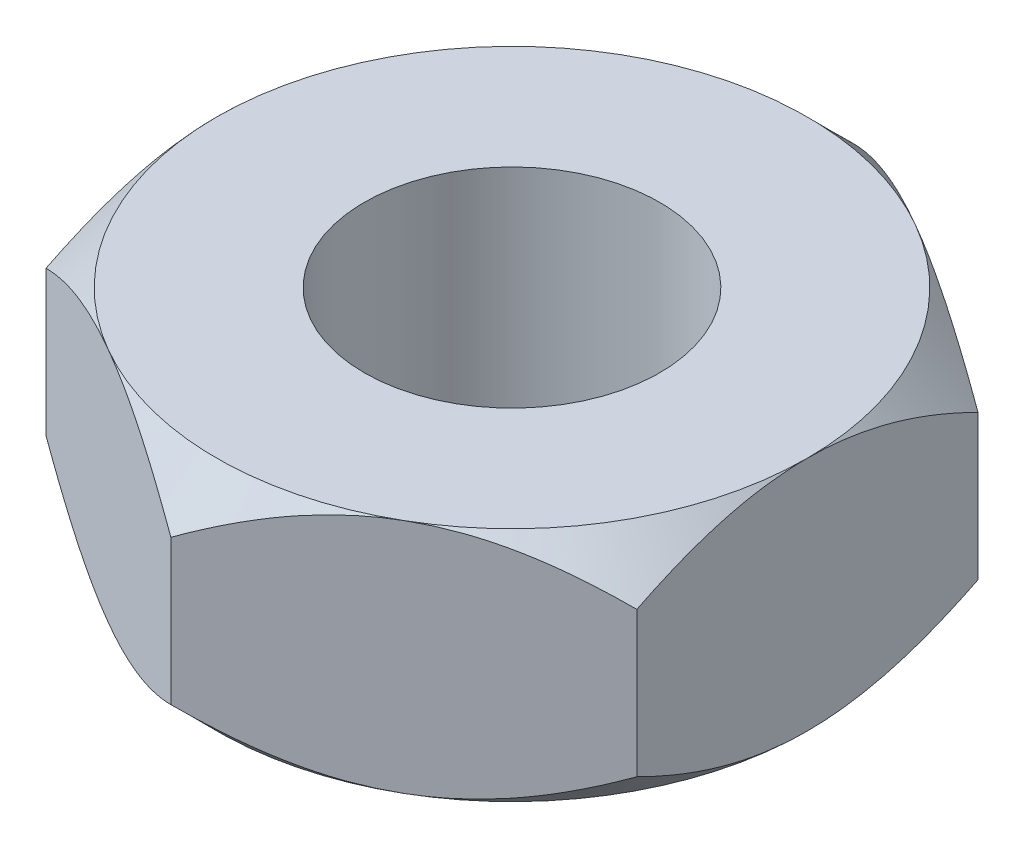
SolidWorks part; units mm, degrees
material "1023 Carbon Steel Sheet (SS)"
ref_plane "Front Plane" through (0, 0, 0) normal (0, 0, 1) x (1, 0, 0)
ref_plane "Top Plane" through (0, 0, 0) normal (0, 1, 0) x (1, 0, 0)
ref_plane "Right Plane" through (0, 0, 0) normal (1, 0, 0) x (0, 0, -1)
sketch "Sketch1" plane through (0, 0, 0) normal (0, 1, 0) x (1, 0, 0)
  line L1 (0, 2.3094) -> (-2, 1.1547)
  line L2 (-2, 1.1547) -> (-2, -1.1547)
  line L3 (-2, -1.1547) -> (0, -2.3094)
  line L4 (0, -2.3094) -> (2, -1.1547)
  line L5 (2, -1.1547) -> (2, 1.1547)
  line L6 (2, 1.1547) -> (0, 2.3094)
  circle A0 centre (0, 0) radius 2 construction
  circle A1 centre (0, 0) radius 1
  dimension "D2" = 2
  dimension "D1" = 4
extrude "Boss-Extrude1" add sketch "Sketch1" along normal blind 1.6
sketch "Sketch2" plane through (0, 1.6, 0) normal (0, 1, 0) x (1, 0, 0)
  circle A0 centre (0, 0) radius 2
  dimension "D1" = 4
extrude "Cut-Extrude1" cut sketch "Sketch2" against normal through all draft 45 flip side to cut
sketch "Sketch3" plane through (0, 0, 0) normal (0, -1, 0) x (1, 0, 0)
  circle A0 centre (0, 0) radius 2
  dimension "D1" = 4
extrude "Cut-Extrude2" cut sketch "Sketch3" against normal through all draft 45 flip side to cut
